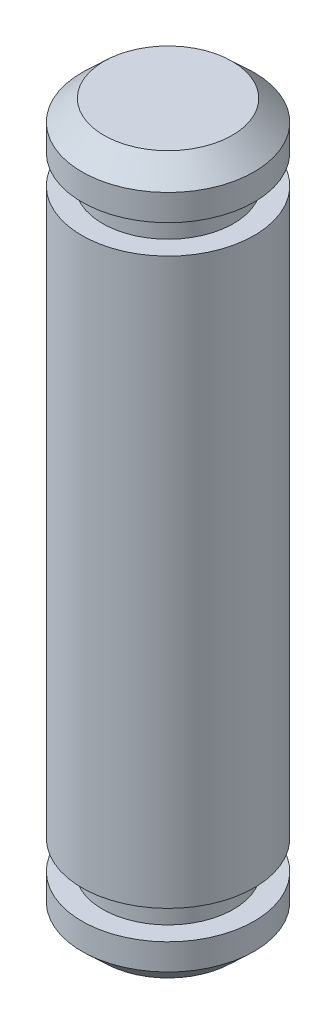
SolidWorks part; units mm, degrees
ref_plane "Front Plane" through (0, 0, 0) normal (0, 0, 1) x (1, 0, 0)
ref_plane "Top Plane" through (0, 0, 0) normal (0, 1, 0) x (1, 0, 0)
ref_plane "Right Plane" through (0, 0, 0) normal (1, 0, 0) x (0, 0, -1)
sketch "Sketch2" plane through (0, 0, 0) normal (0, 0, 1) x (1, 0, 0)
  line L0 (0, 0) -> (0, 17.0045) construction
  line L1 (-1.5875, -5.207) -> (-1.5875, 5.207)
  line L2 (-1.5875, 5.207) -> (-1.2065, 5.207)
  line L3 (-1.2065, 5.207) -> (-1.2065, 5.7404)
  line L4 (-1.2065, 5.7404) -> (-1.5875, 5.7404)
  line L5 (-1.5875, 5.7404) -> (-1.5875, 6.223)
  line L6 (-1.5875, 6.223) -> (-1.1828, 6.604)
  line L7 (-1.1828, 6.604) -> (0, 6.604)
  line L8 (0, 6.604) -> (0, -6.604)
  line L9 (0, 0) -> (-14.3814, 0) construction
  line L10 (-1.1828, -6.604) -> (0, -6.604)
  line L11 (-1.5875, -6.223) -> (-1.1828, -6.604)
  line L12 (-1.5875, -5.7404) -> (-1.5875, -6.223)
  line L13 (-1.2065, -5.7404) -> (-1.5875, -5.7404)
  line L14 (-1.2065, -5.207) -> (-1.2065, -5.7404)
  line L15 (-1.5875, -5.207) -> (-1.2065, -5.207)
  point P19 (-1.5875, 0)
  dimension "D1" = 3.175
  dimension "D2" = 2.413
  dimension "D3" = 3.175
  dimension "D4" = 3.175
  dimension "D5" = 0.5334
  dimension "D6" = 5.207
  dimension "D7" = 6.604
  dimension "D8" = 0.381
revolve "Revolve4" add sketch "Sketch2" angle 360 about L0
